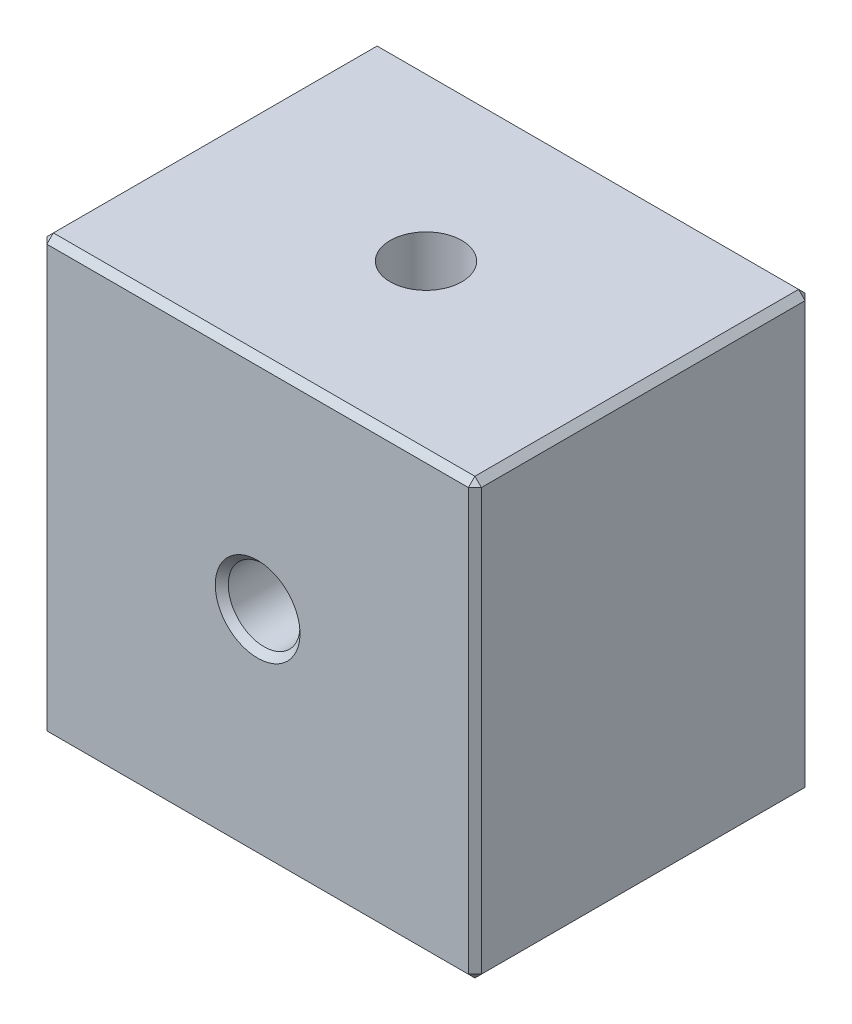
SolidWorks part; units mm, degrees
material "6061 合金"
ref_plane "前视基准面" through (0, 0, 0) normal (0, 0, 1) x (1, 0, 0)
ref_plane "上视基准面" through (0, 0, 0) normal (0, 1, 0) x (1, 0, 0)
ref_plane "右视基准面" through (0, 0, 0) normal (1, 0, 0) x (0, 0, -1)
sketch "草图1" plane through (0, 0, 0) normal (0, 0, 1) x (1, 0, 0)
  line L1 (-10, -10) -> (10, -10)
  line L2 (-10, -10) -> (-10, 10)
  line L3 (-10, 10) -> (10, 10)
  line L4 (10, -10) -> (10, 10)
  line L5 (0, 10) -> (0, -10) construction
  line L6 (-10, 0) -> (10, 0) construction
  point P0 (0, 0)
  dimension "D1" = 20
  dimension "D2" = 20
extrude "凸台-拉伸1" add sketch "草图1" along normal mid plane 15.5
hole_wizard "M4 螺纹孔1" positions "草图2" profile "草图3" tap size "M4" standard "GB" end condition through all
sketch "草图2" plane through (0, 0, 7.75) normal (0, 0, 1) x (1, 0, 0)
  point P0 (0, 0)
sketch "草图3" plane through (0, 0, 7.75) normal (1, 0, 0) x (0, -1, 0)
  line L0 (0, 0) -> (0, 15.5)
  line L1 (0, 15.5) -> (1.65, 15.5)
  line L2 (1.65, 15.5) -> (1.65, 0)
  line L5 (1.65, 0) -> (0, 0)
  line L11 (0, -6.35) -> (0, 107.95) construction
  dimension "通孔螺纹孔钻头直径" = 3.3
  dimension "通孔螺纹孔钻头深度" = 15.5
cosmetic thread "孔螺蚊线1" parameters "D2"=4
hole_wizard "M4 螺纹孔2" positions "草图5" profile "草图6" tap size "M4" standard "GB" end condition through all
sketch "草图5" plane through (0, 10, 0) normal (0, 1, 0) x (1, 0, 0)
  point P0 (0, 0)
sketch "草图6" plane through (0, 10, 0) normal (1, 0, 0) x (0, 0, 1)
  line L0 (0, 0) -> (0, 20)
  line L1 (0, 20) -> (1.65, 20)
  line L2 (1.65, 20) -> (1.65, 0)
  line L5 (1.65, 0) -> (0, 0)
  line L11 (0, -6.35) -> (0, 107.95) construction
  dimension "通孔螺纹孔钻头直径" = 3.3
  dimension "通孔螺纹孔钻头深度" = 20
cosmetic thread "孔螺蚊线2" parameters "D2"=4
chamfer "倒角1" distance 0.3 angle 45 13 edges at (1.65, 0, 7.75) (-10, 10, 0) (0, 10, -7.75) (10, -10, 0) (10, 10, 0) (10, 0, -7.75) (0, -10, 7.75) (10, 0, 7.75) (0, 10, 7.75) (-10, 0, 7.75) (-10, 0, -7.75) (-10, -10, 0) (0, -10, -7.75)
